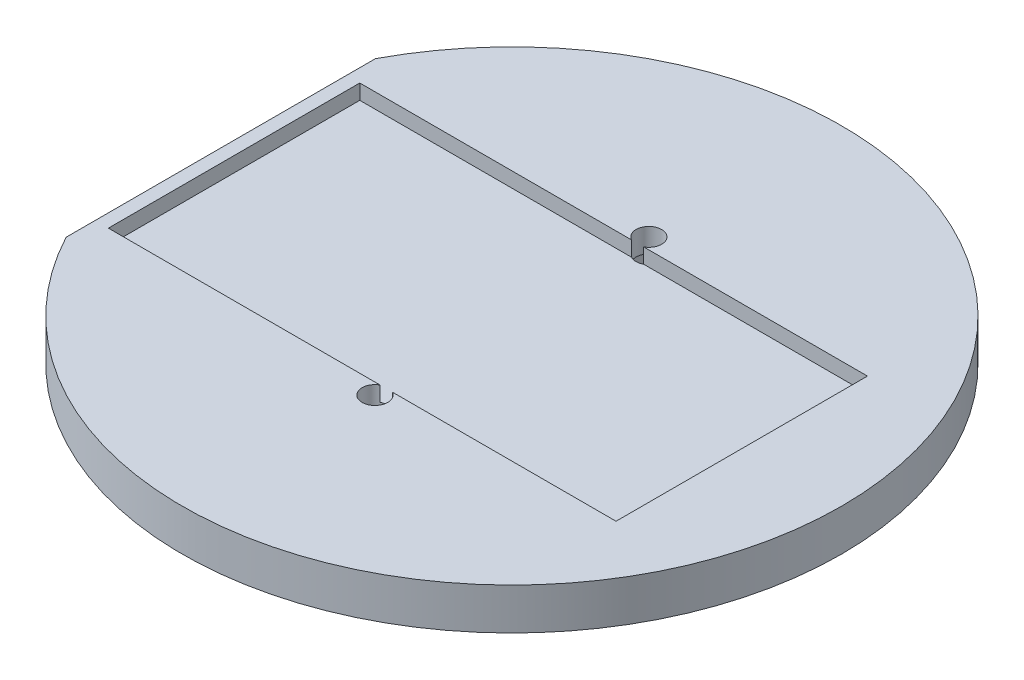
SolidWorks part; units mm, degrees
ref_plane "Front Plane" through (0, 0, 0) normal (0, 0, 1) x (1, 0, 0)
ref_plane "Top Plane" through (0, 0, 0) normal (0, 1, 0) x (1, 0, 0)
ref_plane "Right Plane" through (0, 0, 0) normal (1, 0, 0) x (0, 0, -1)
sketch "Sketch1" plane through (0, 0, 0) normal (0, 1, 0) x (1, 0, 0)
  line L0 (-32.9399, 17.5) -> (-32.9399, -17.5)
  arc A1 (-32.9399, -17.5) -> (-32.9399, 17.5) centre (0, 0) ccw
  dimension "D1" = 74.6
  dimension "D2" = 35
extrude "Boss-Extrude1" add sketch "Sketch1" along normal blind 3
sketch "Sketch2" plane through (0, 3, 0) normal (0, 1, 0) x (1, 0, 0)
  line L0 (-32.9399, 17.5) -> (-32.9399, -17.5) construction
  line L1 (-32.9399, 17.5) -> (-32.9399, -17.5)
  line L3 (26.0101, -14.225) -> (-31.4399, -14.225)
  line L4 (26.0101, -14.225) -> (26.0101, 14.225)
  line L5 (26.0101, 14.225) -> (-31.4399, 14.225)
  line L6 (-31.4399, -14.225) -> (-31.4399, 14.225)
  line L7 (26.0101, -14.225) -> (-31.4399, 14.225) construction
  line L8 (26.0101, 14.225) -> (-31.4399, -14.225) construction
  arc A0 (-32.9399, -17.5) -> (-32.9399, 17.5) centre (0, 0) ccw construction
  arc A1 (-32.9399, -17.5) -> (-32.9399, 17.5) centre (0, 0) ccw
  point P3 (-2.7149, 0)
  point P8 (0, 0)
  dimension "D1" = 1.5
  dimension "D2" = 57.45
  dimension "D3" = 28.45
extrude "Boss-Extrude2" add sketch "Sketch2" along normal blind 1.7
sketch "Sketch3" plane through (0, 4.7, 0) normal (0, 1, 0) x (1, 0, 0)
  circle A0 centre (0, 15.5) radius 1.45
  dimension "D1" = 2.9
  dimension "D2" = 15.5
extrude "Cut-Extrude1" cut sketch "Sketch3" against normal through all
sketch "Sketch4" plane through (0, 0, 0) normal (0, -1, 0) x (1, 0, 0)
  line L1 (2.8868, -15.5) -> (1.4434, -13)
  line L2 (1.4434, -13) -> (-1.4434, -13)
  line L3 (-1.4434, -13) -> (-2.8868, -15.5)
  line L4 (-2.8868, -15.5) -> (-1.4434, -18)
  line L5 (-1.4434, -18) -> (1.4434, -18)
  line L6 (1.4434, -18) -> (2.8868, -15.5)
  circle A0 centre (0, -15.5) radius 2.5 construction
  dimension "D1" = 5
extrude "Cut-Extrude2" cut sketch "Sketch4" against normal blind 2
mirror "Mirror2" about plane through (0, 0, 0) normal (0, 0, 1) of "Cut-Extrude2", "Cut-Extrude1"
